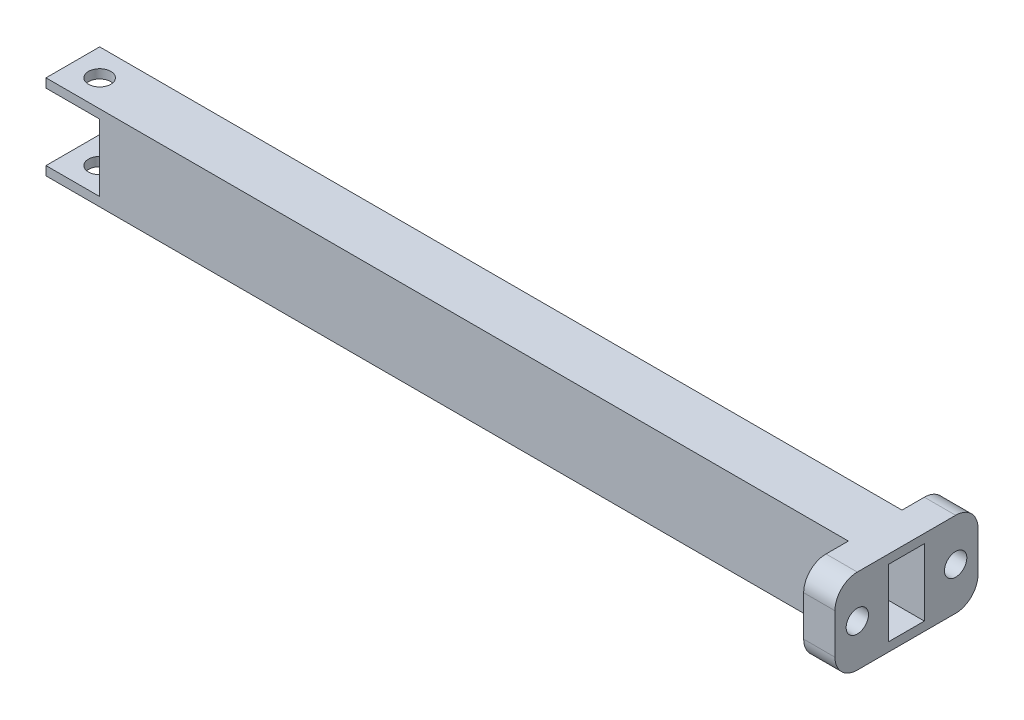
SolidWorks part; units mm, degrees
ref_plane "Alzado" through (0, 0, 0) normal (0, 0, 1) x (1, 0, 0)
ref_plane "Planta" through (0, 0, 0) normal (0, 1, 0) x (1, 0, 0)
ref_plane "Vista lateral" through (0, 0, 0) normal (1, 0, 0) x (0, 0, -1)
sketch "Croquis1" plane through (0, 0, 0) normal (1, 0, 0) x (0, 0, -1)
  line L1 (-6, -9.5) -> (6, -9.5)
  line L2 (-6, -9.5) -> (-6, 9.5)
  line L3 (-6, 9.5) -> (6, 9.5)
  line L4 (6, -9.5) -> (6, 9.5)
  line L5 (-6, -9.5) -> (6, 9.5) construction
  line L6 (-6, 9.5) -> (6, -9.5) construction
  line L7 (-4, -7.5) -> (4, -7.5)
  line L8 (-4, -7.5) -> (-4, 7.5)
  line L9 (-4, 7.5) -> (4, 7.5)
  line L10 (4, -7.5) -> (4, 7.5)
  line L11 (-4, -7.5) -> (4, 7.5) construction
  line L12 (-4, 7.5) -> (4, -7.5) construction
  point P0 (0, 0)
  point P7 (0, 0)
  dimension "D1" = 12
  dimension "D2" = 19
  dimension "D3" = 2
  dimension "D4" = 2
extrude "Saliente-Extruir1" add sketch "Croquis1" along normal mid plane 373
sketch "Croquis2" plane through (0, 0, 6) normal (0, 0, 1) x (1, 0, 0)
  line L0 (-186.5, 9.5) -> (-186.5, -9.5) construction
  line L1 (-186.5, 7.5) -> (-174.5, 7.5)
  line L2 (-186.5, 7.5) -> (-186.5, -7.5)
  line L3 (-186.5, -7.5) -> (-174.5, -7.5)
  line L4 (-174.5, 7.5) -> (-174.5, -7.5)
  line L5 (186.5, 9.5) -> (186.5, -9.5) construction
  line L6 (186.5, 7.5) -> (174.5, 7.5)
  line L7 (186.5, 7.5) -> (186.5, -7.5)
  line L8 (186.5, -7.5) -> (174.5, -7.5)
  line L9 (174.5, 7.5) -> (174.5, -7.5)
  line L10 (186.5, 9.5) -> (-186.5, 9.5) construction
  line L11 (186.5, -9.5) -> (-186.5, -9.5) construction
  dimension "D1" = 2
  dimension "D2" = 2
  dimension "D3" = 12
  dimension "D4" = 2
  dimension "D5" = 2
  dimension "D6" = 12
extrude "Cortar-Extruir1" cut sketch "Croquis2" against normal blind 12
sketch "Croquis3" plane through (0, 9.5, 0) normal (0, 1, 0) x (1, 0, 0)
  line L0 (-186.5, 0) -> (-180.5, 0) construction
  line L1 (-186.5, 6) -> (-186.5, -6) construction
  line L2 (186.5, 0) -> (180.5, 0) construction
  line L3 (186.5, 6) -> (186.5, -6) construction
  circle A0 centre (-180.5, 0) radius 2.5
  circle A1 centre (180.5, 0) radius 2.5
  dimension "D1" = 5
  dimension "D4" = 5
  dimension "D2" = 6
  dimension "D3" = 6
extrude "Cortar-Extruir2" cut sketch "Croquis3" against normal blind 19
sketch "Sketch1" plane through (0, 0, 6) normal (0, 0, 1) x (1, 0, 0)
  line L0 (186.5, -9.5) -> (-186.5, -9.5) construction
  line L1 (0, -9.5) -> (186.5, -9.5)
  line L2 (0, -9.5) -> (0, 9.5)
  line L3 (0, 9.5) -> (186.5, 9.5)
  line L4 (186.5, -9.5) -> (186.5, 9.5)
extrude "Cut-Extrude1" cut sketch "Sketch1" against normal through all
sketch "Sketch2" plane through (0, 0, 6) normal (0, 0, 1) x (1, 0, 0)
  line L0 (0, 9.5) -> (-186.5, 9.5) construction
  line L1 (0, -9.5) -> (-7, -9.5)
  line L2 (0, -9.5) -> (0, 9.5)
  line L3 (0, 9.5) -> (-7, 9.5)
  line L4 (-7, -9.5) -> (-7, 9.5)
  dimension "D1" = 7
extrude "Boss-Extrude1" add sketch "Sketch2" along normal blind 10
sketch "Sketch3" plane through (0, 0, 0) normal (1, 0, 0) x (0, 0, -1)
  line L0 (-16, -9.5) -> (-16, 9.5) construction
  line L2 (6, 9.5) -> (-16, 9.5) construction
  circle A0 centre (-11, 0) radius 2.5
  point P6 (-8.9145, 9.5)
  dimension "D1" = 5
  dimension "D2" = 5
  dimension "D3" = 9.5
extrude "Cut-Extrude2" cut sketch "Sketch3" against normal blind 10
fillet "Fillet1" radius 5 2 edges at (-3.5, -9.5, 16) (-3.5, 9.5, 16)
mirror "Mirror1" about plane through (0, 0, 0) normal (0, 0, 1) of "Boss-Extrude1", "Cut-Extrude2"
fillet "Fillet2" radius 5 2 edges at (-3.5, -9.5, -16) (-3.5, 9.5, -16)
